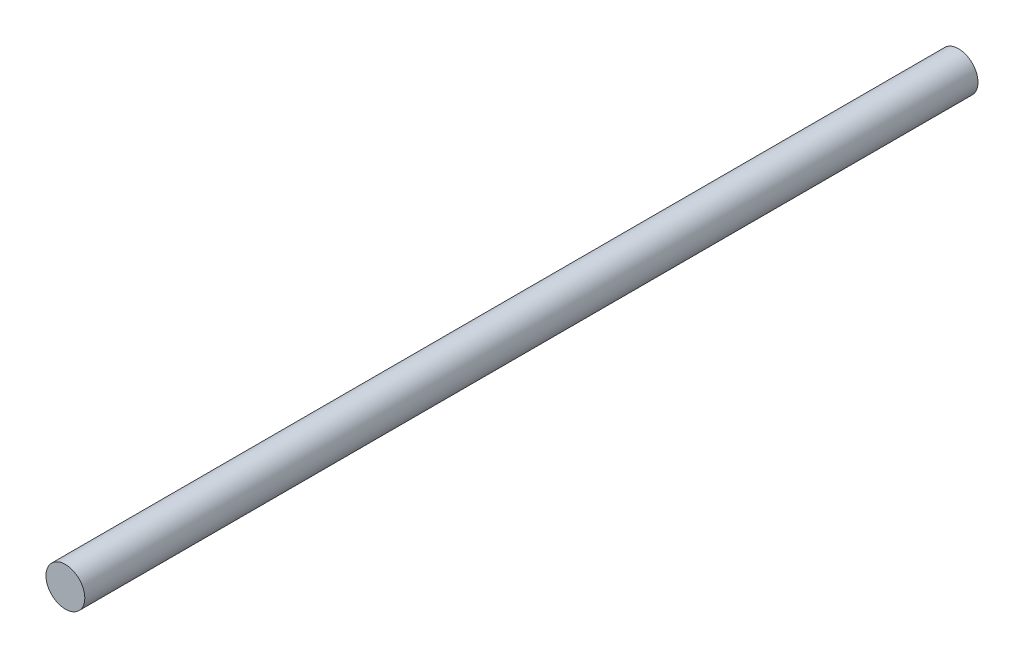
SolidWorks part; units mm, degrees
material "1023 Carbon Steel Sheet (SS)"
ref_plane "Front Plane" through (0, 0, 0) normal (0, 0, 1) x (1, 0, 0)
ref_plane "Top Plane" through (0, 0, 0) normal (0, 1, 0) x (1, 0, 0)
ref_plane "Right Plane" through (0, 0, 0) normal (1, 0, 0) x (0, 0, -1)
sketch "Sketch1" plane through (0, 0, 0) normal (0, 0, 1) x (1, 0, 0)
  circle A0 centre (0, 0) radius 6.35
  dimension "D1" = 12.7
extrude "Boss-Extrude1" add sketch "Sketch1" along normal mid plane 292.1
